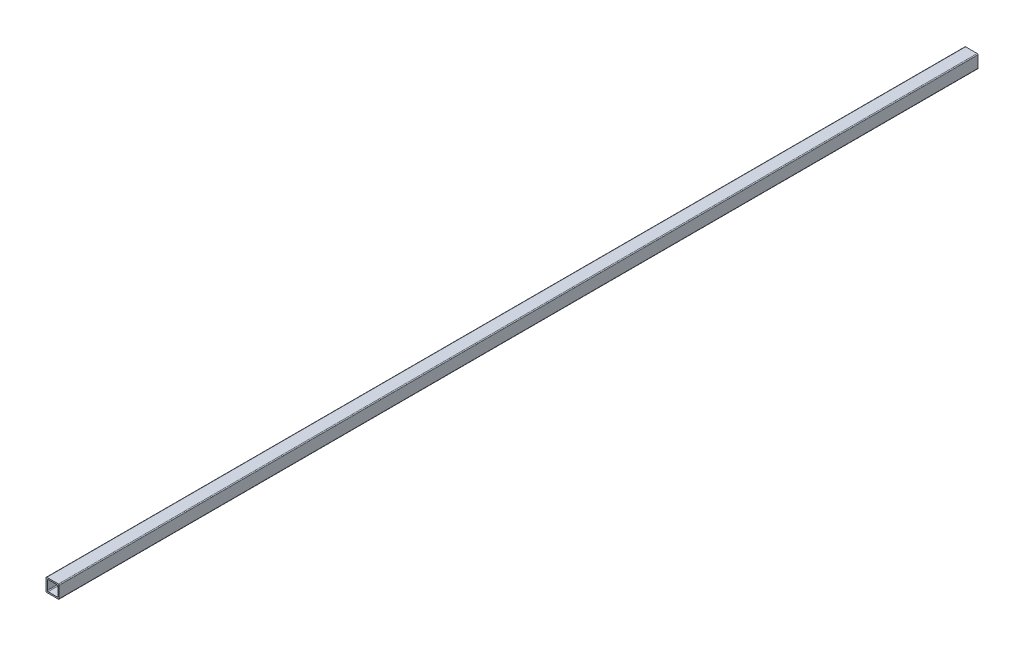
SolidWorks part; units mm, degrees
material "Hexcel AS4C (3000 Filaments)"
ref_plane "Front Plane" through (0, 0, 0) normal (0, 0, 1) x (1, 0, 0)
ref_plane "Top Plane" through (0, 0, 0) normal (0, 1, 0) x (1, 0, 0)
ref_plane "Right Plane" through (0, 0, 0) normal (1, 0, 0) x (0, 0, -1)
sketch "Sketch1" plane through (0, 0, 0) normal (0, 0, 1) x (1, 0, 0)
  line L1 (-3.95, 3.95) -> (3.95, 3.95)
  line L2 (-3.95, 3.95) -> (-3.95, -3.95)
  line L3 (-3.95, -3.95) -> (3.95, -3.95)
  line L4 (3.95, 3.95) -> (3.95, -3.95)
  line L5 (-3.95, 3.95) -> (3.95, -3.95) construction
  line L6 (-3.95, -3.95) -> (3.95, 3.95) construction
  line L7 (-3.15, 3.15) -> (3.15, 3.15)
  line L8 (-3.15, 3.15) -> (-3.15, -3.15)
  line L9 (-3.15, -3.15) -> (3.15, -3.15)
  line L10 (3.15, 3.15) -> (3.15, -3.15)
  line L11 (-3.15, 3.15) -> (3.15, -3.15) construction
  line L12 (-3.15, -3.15) -> (3.15, 3.15) construction
  point P0 (0, 0)
  point P6 (0, 0)
  dimension "D1" = 7.9
  dimension "D2" = 0.8
extrude "Boss-Extrude1" add sketch "Sketch1" along normal mid plane 550
fillet "Fillet1" radius 0.5 8 edges at (3.95, 3.95, 0) (3.15, 3.15, 0) (3.95, -3.95, 0) (3.15, -3.15, 0) (-3.95, -3.95, 0) (-3.15, -3.15, 0) (-3.15, 3.15, 0) (-3.95, 3.95, 0)
